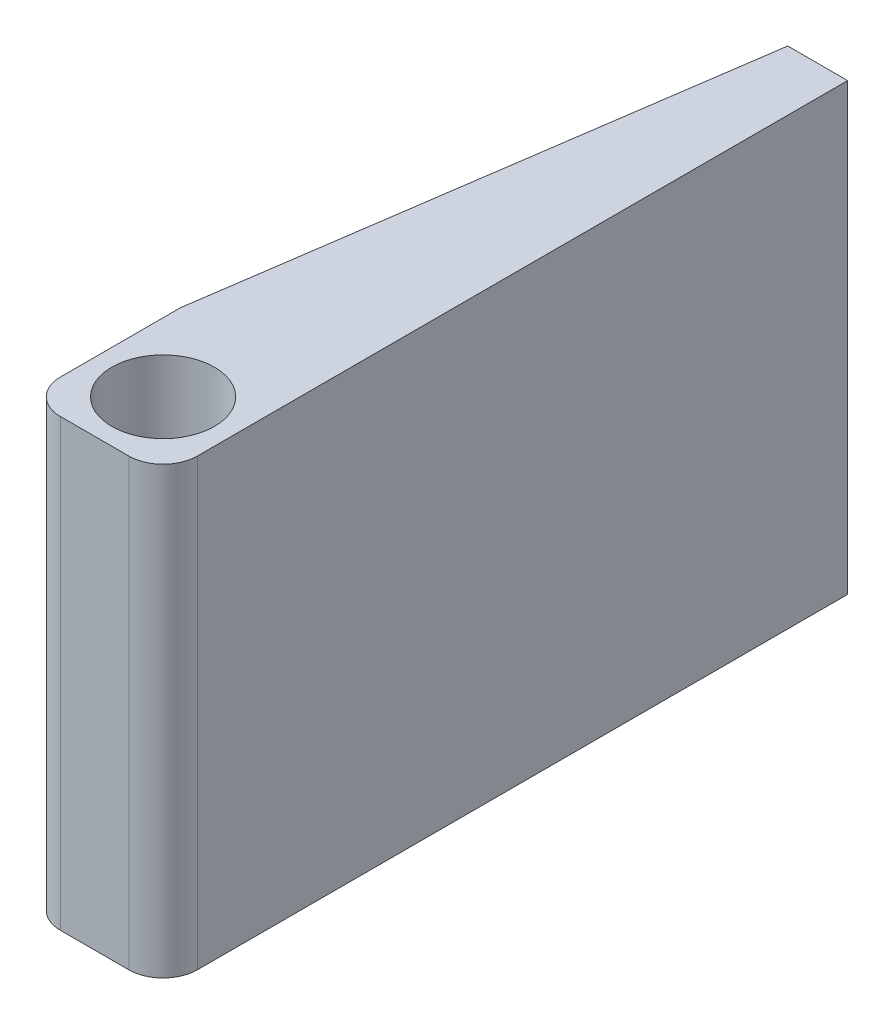
SolidWorks part; units mm, degrees
ref_plane "Front Plane" through (0, 0, 0) normal (0, 0, 1) x (1, 0, 0)
ref_plane "Top Plane" through (0, 0, 0) normal (0, 1, 0) x (1, 0, 0)
ref_plane "Right Plane" through (0, 0, 0) normal (1, 0, 0) x (0, 0, -1)
sketch "Sketch2" plane through (0, 0, 0) normal (1, 0, 0) x (0, 0, -1)
  line L1 (-155.3642, 198.3449) -> (352.6358, 198.3449)
  line L2 (-155.3642, 198.3449) -> (-155.3642, -131.8551)
  line L3 (-155.3642, -131.8551) -> (352.6358, -131.8551)
  line L4 (352.6358, 198.3449) -> (352.6358, -131.8551)
  dimension "D1" = 508
  dimension "D2" = 330.2
extrude "Boss-Extrude1" add sketch "Sketch2" along normal blind 101.6
sketch "Sketch3" plane through (0, -131.8551, 0) normal (0, -1, 0) x (1, 0, 0)
  line L0 (101.6, 155.3642) -> (101.6, -352.6358) construction
  line L2 (101.6, 155.3642) -> (0, 155.3642) construction
  circle A0 centre (50.8, 104.5642) radius 38.1
  point P6 (-32.5752, 35.7891)
  point P7 (215.5938, 61.64)
  dimension "D1" = 50.8
  dimension "D3" = 76.2
  dimension "D2" = 50.8
extrude "Cut-Extrude1" cut sketch "Sketch3" against normal through all
fillet "Fillet1" radius 25.4 2 edges at (0, 33.2449, 155.3642) (101.6, 33.2449, 155.3642)
sketch "Sketch4" plane through (0, -131.8551, 0) normal (0, -1, 0) x (1, 0, 0)
  line L0 (0, 40.9592) -> (57.15, -352.6358)
  line L1 (0, 129.9642) -> (0, -352.6358) construction
  line L2 (101.6, -352.6358) -> (0, -352.6358) construction
  line L3 (57.15, -352.6358) -> (0, -352.6358)
  line L4 (0, -352.6358) -> (0, 40.9592)
  dimension "D1" = 44.45
extrude "Cut-Extrude2" cut sketch "Sketch4" against normal through all
sketch "Sketch5" plane through (0, 0, -352.6358) normal (0, 0, -1) x (-1, 0, 0)
  line L0 (-101.6, -131.8551) -> (-101.6, 198.3449) construction
  line L1 (-91.44, 71.3449) -> (-68.3357, 71.3449)
  line L2 (-91.44, 71.3449) -> (-91.44, -4.8551)
  line L3 (-91.44, -4.8551) -> (-68.3357, -4.8551)
  line L4 (-68.3357, 71.3449) -> (-68.3357, -4.8551)
  line L5 (-101.6, 198.3449) -> (-57.15, 198.3449) construction
  line L6 (-101.6, -131.8551) -> (-57.15, -131.8551) construction
  point P4 (-91.44, 33.2449)
  point P7 (-101.6, 33.2449)
  dimension "D1" = 10.16
  dimension "D2" = 127
  dimension "D3" = 127
extrude "Cut-Extrude3" cut sketch "Sketch5" against normal blind 50.8
